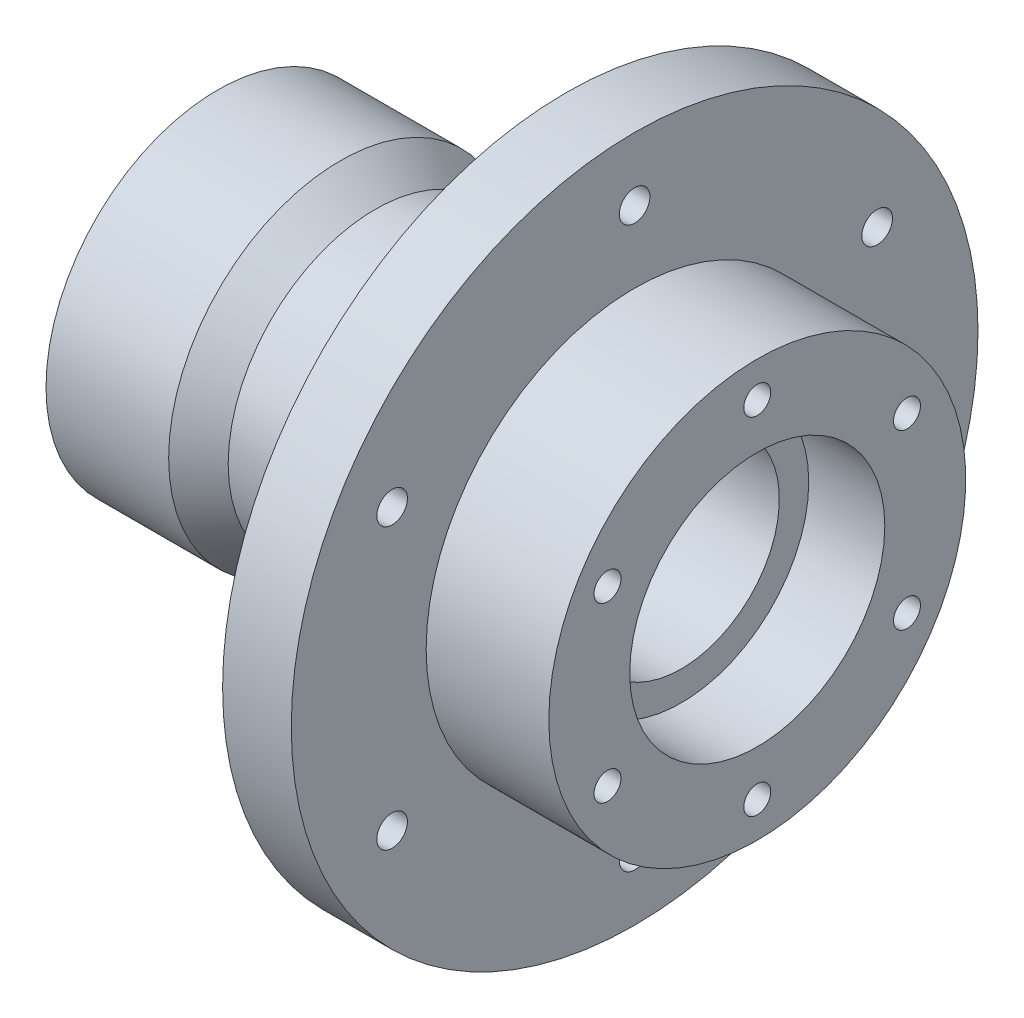
SolidWorks part; units mm, degrees
ref_plane "Piano frontale" through (0, 0, 0) normal (0, 0, 1) x (1, 0, 0)
ref_plane "Piano superiore" through (0, 0, 0) normal (0, 1, 0) x (1, 0, 0)
ref_plane "Piano destro" through (0, 0, 0) normal (1, 0, 0) x (0, 0, -1)
sketch "Schizzo1" plane through (0, 0, 0) normal (0, 0, 1) x (1, 0, 0)
  line L0 (-27.2255, 20) -> (49.4245, 20)
  line L1 (49.4245, 20) -> (49.4245, 26)
  line L2 (49.4245, 26) -> (64.9245, 26)
  line L3 (64.9245, 26) -> (64.9245, 42.5)
  line L4 (64.9245, 42.5) -> (39.9245, 42.5)
  line L5 (39.9245, 42.5) -> (39.9245, 70)
  line L6 (39.9245, 70) -> (25.9245, 70)
  line L7 (25.9245, 70) -> (25.9245, 30)
  line L8 (25.9245, 30) -> (-12.9347, 30)
  line L9 (-12.9347, 30) -> (-20.0755, 35)
  line L10 (-20.0755, 35) -> (-45.0755, 35)
  line L11 (-45.0755, 35) -> (-45.0755, 23.5)
  line L12 (-45.0755, 23.5) -> (-43.0755, 23.5)
  line L13 (-43.0755, 23.5) -> (-43.0755, 24.75)
  line L14 (-43.0755, 24.75) -> (-41.2255, 24.75)
  line L17 (-41.2255, 24.75) -> (-41.2255, 23.5)
  line L18 (-41.2255, 23.5) -> (-27.2255, 23.5)
  line L19 (-27.2255, 23.5) -> (-27.2255, 20)
  dimension "D1" = 14
  dimension "D2" = 25
  dimension "D3" = 71
  dimension "D4" = 25
  dimension "D5" = 20
  dimension "D6" = 30
  dimension "D7" = 15.5
  dimension "D8" = 35
  dimension "D9" = 23.5
  dimension "D10" = 23.5
  dimension "D11" = 24.75
  dimension "D12" = 2
  dimension "D13" = 1.85
  dimension "D14" = 17.85
  dimension "D15" = 110
  dimension "D16" = 26
  dimension "D17" = 42.5
  dimension "D18" = 70
  dimension "D19" = 16.5
ref_axis "Assi1" through (0, 0, 0) along (1, 0, 0)
revolve "Rivoluzione1" add sketch "Schizzo1" angle 360 about axis through (0, 0, 0) along (1, 0, 0)
sketch "Schizzo2" plane through (39.9245, 0, 0) normal (1, 0, 0) x (0, 0, -1)
  circle A0 centre (0, 57.09) radius 3.125
  dimension "D1" = 57.09
  dimension "D3" = 6.25
  dimension "D2" = 0
extrude "Taglio-Estrusione1" cut sketch "Schizzo2" against normal up to surface (14 mm away) up to face at (25.9245, 0, 30)
hole_wizard "Foro per Vite M5-1" positions "Schizzo4" profile "Schizzo5" hole size "M5" standard "ISO"
sketch "Schizzo4" plane through (64.9245, 0, 0) normal (1, 0, 0) x (0, 0, -1)
  point P0 (0, 35.25)
  dimension "D1" = 35.25
sketch "Schizzo5" plane through (64.9245, 35.25, 0) normal (0, 1, 0) x (0, 0, -1)
  line L0 (0, 0) -> (0, 12)
  line L1 (0, 12) -> (2.75, 10.3476)
  line L2 (2.75, 10.3476) -> (2.75, 0)
  line L5 (2.75, 0) -> (0, 0)
  line L10 (0, 12) -> (-2.75, 10.3476) construction
  line L11 (0, -6.35) -> (0, 107.95) construction
  dimension "Hole Dia." = 5.5
  dimension "Hole Depth" = 12
  dimension "Drill Angle" = 118
pattern_circular "RipetizioneCircolare1" count 6 over 360 about axis through (0, 0, 0) along (1, 0, 0) of "Foro per Vite M5-1", "Taglio-Estrusione1"
fillet "Raccordo1" radius 3 1 edges at (25.9245, 0, 30)
